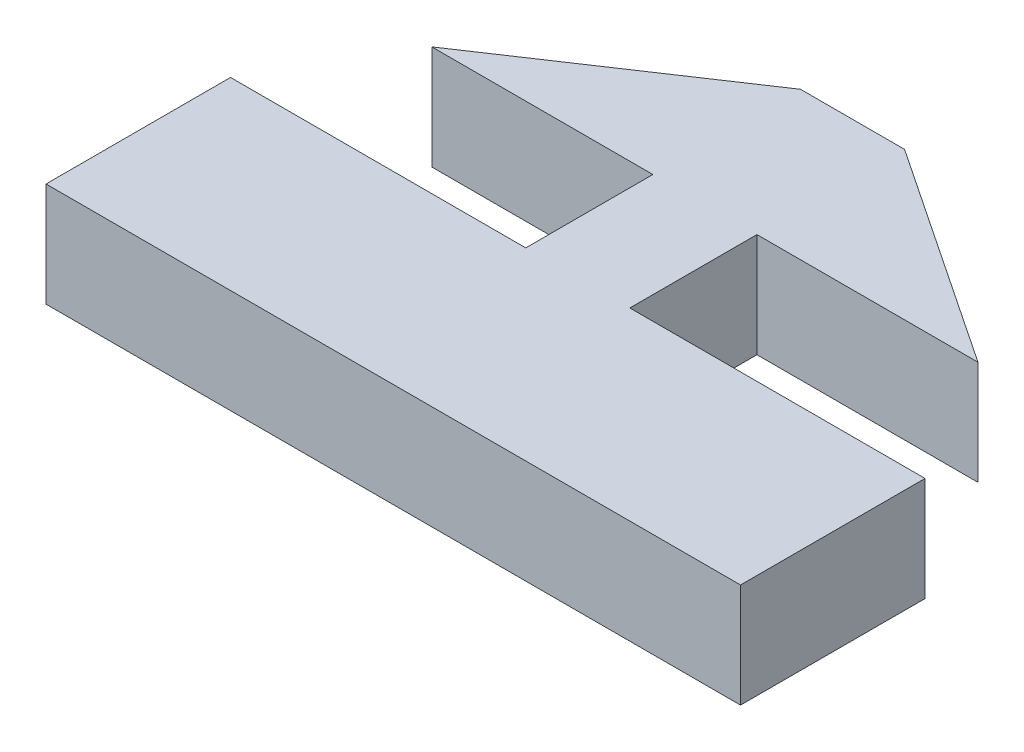
SolidWorks part; units mm, degrees
ref_plane "Front" through (0, 0, 0) normal (0, 0, 1) x (1, 0, 0)
ref_plane "Top" through (0, 0, 0) normal (0, 1, 0) x (1, 0, 0)
ref_plane "Right" through (0, 0, 0) normal (1, 0, 0) x (0, 0, -1)
sketch "Sketch1" plane through (0, 0, 0) normal (0, 1, 0) x (1, 0, 0)
  line L0 (-1.7907, 2.1875) -> (-9.398, 2.1875)
  line L2 (-1.7907, -2.1875) -> (-1.7907, 2.1875)
  line L4 (1.7907, -2.1875) -> (1.7907, 2.1875)
  line L7 (-9.398, 2.1875) -> (-1.7907, 7.2675)
  line L8 (-1.7907, 7.2675) -> (1.7907, 7.2675)
  line L9 (1.7907, 7.2675) -> (9.398, 2.1875)
  line L10 (9.398, 2.1875) -> (1.7907, 2.1875)
  line L11 (1.7907, -2.1875) -> (11.9507, -2.1875)
  line L12 (-1.7907, -2.1875) -> (-11.9507, -2.1875)
  line L13 (-11.9507, -2.1875) -> (-11.9507, -8.5375)
  line L14 (-11.9507, -8.5375) -> (11.9507, -8.5375)
  line L15 (11.9507, -8.5375) -> (11.9507, -2.1875)
  line L16 (11.9507, -2.1875) -> (1.7907, -2.1875)
  point P0 (0, 0)
  point P17 (0, 7.2675)
  point P19 (0, -8.5375)
  point P24 (1.7907, 0)
  dimension "D1" = 18.796
  dimension "D2" = 3.5814
  dimension "D3" = 10.16
  dimension "D4" = 6.35
  dimension "D5" = 5.08
  dimension "D7" = 4.375
extrude "Boss-Extrude1" add sketch "Sketch1" along normal blind 3.5814 contours L14 L15 L11 L4 L10 L9 L8 L7 L0 L2 L12 L13
